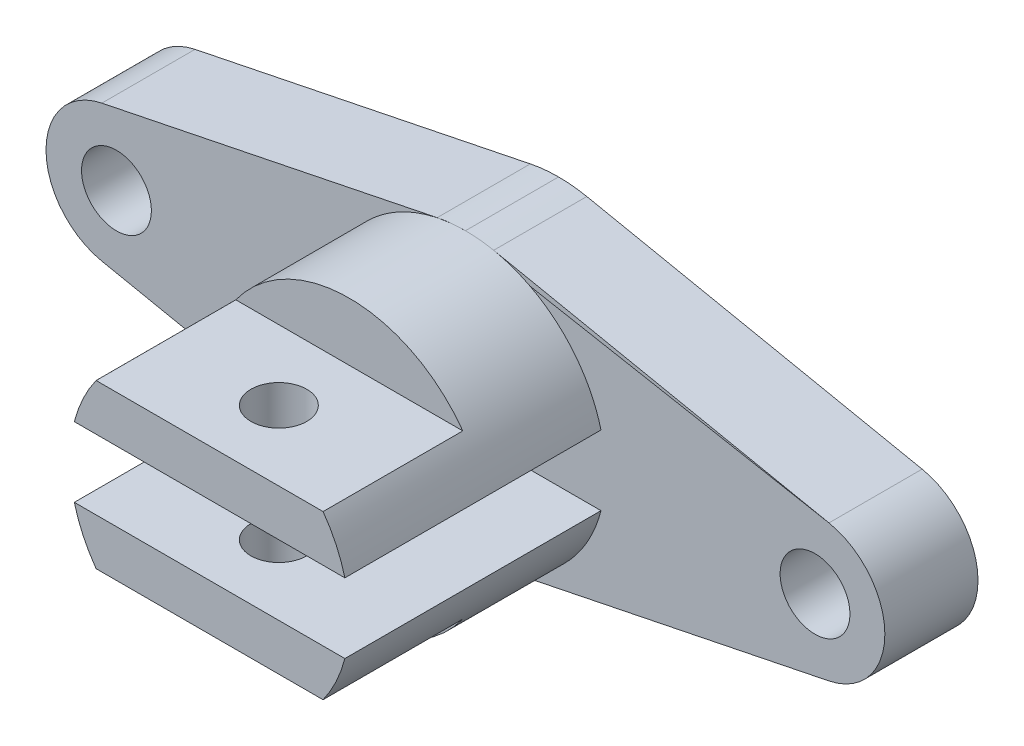
SolidWorks part; units mm, degrees
ref_plane "Alzado" through (0, 0, 0) normal (0, 0, 1) x (1, 0, 0)
ref_plane "Planta" through (0, 0, 0) normal (0, 1, 0) x (1, 0, 0)
ref_plane "Vista lateral" through (0, 0, 0) normal (1, 0, 0) x (0, 0, -1)
sketch "Croquis1" plane through (0, 0, 0) normal (0, 0, 1) x (1, 0, 0)
  line L0 (153, 14.6969) -> (81, 29.3939)
  line L1 (153, -14.6969) -> (81, -29.3939)
  line L4 (81, 29.3939) -> (81, -29.3939) construction
  line L5 (153, 14.6969) -> (153, -14.6969) construction
  line L10 (68.8736, 29.3678) -> (68.8736, -29.3678) construction
  line L11 (74.9354, 29.9999) -> (74.9354, -29.9999) construction
  line L12 (68.8709, 29.3939) -> (68.8709, -29.3939) construction
  line L13 (-3.1291, 14.6969) -> (68.8709, 29.3939)
  line L14 (-3.1291, 14.6969) -> (-3.1291, -14.6969) construction
  line L15 (-3.1291, -14.6969) -> (68.8709, -29.3939)
  circle A2 centre (150, 0) radius 7.5
  arc A7 (153, -14.6969) -> (153, 14.6969) centre (150, 0) ccw
  arc A8 (74.9354, -29.9999) -> (81, -29.3939) centre (75, 0) ccw
  arc A9 (81, 29.3939) -> (74.9354, 29.9999) centre (75, 0) ccw
  circle A10 centre (-0.1291, 0) radius 7.5
  arc A11 (-3.1291, -14.6969) -> (-3.1291, 14.6969) centre (-0.1291, 0) cw
  arc A12 (74.9354, -29.9999) -> (68.8709, -29.3939) centre (74.8709, 0) cw
  arc A13 (68.8709, 29.3939) -> (74.9354, 29.9999) centre (74.8709, 0) cw
  point P8 (-0.1291, 0)
  dimension "D2" = 15
  dimension "D6" = 60
  dimension "D5" = 30
  dimension "D7" = 75
extrude "Saliente-Extruir1" add sketch "Croquis1" along normal blind 20 contours L13 A13 A9 L0 A7 L1 A8 A12 L15 A11
sketch "Croquis3" plane through (0, 0, 20) normal (0, 0, 1) x (1, 0, 0)
  line L1 (45.9527, 7.5) -> (104.0473, 7.5)
  line L3 (45.9527, -7.5) -> (104.0473, -7.5)
  arc A0 (45.9527, -7.5) -> (104.0473, -7.5) centre (75, 0) ccw
  arc A1 (104.0473, 7.5) -> (45.9527, 7.5) centre (75, 0) ccw
  arc A2 (153, -14.6969) -> (153, 14.6969) centre (150, 0) ccw construction
  dimension "D1" = 75
  dimension "D2" = 15
  dimension "D3" = 75
  dimension "D4" = 30
extrude "Saliente-Extruir3" add sketch "Croquis3" along normal blind 55
sketch "Croquis9" plane through (0, 0, 75) normal (0, 0, 1) x (1, 0, 0)
  line L1 (74.9666, -0.0068) -> (75.0027, -0.0005) construction
  line L2 (50.6312, 17.4932) -> (99.3742, 17.4932)
  line L8 (75, -0.0068) -> (75.0027, -0.0005) construction
  line L9 (50.6402, -17.5068) -> (99.3652, -17.5068)
  line L11 (50.6312, 17.4932) -> (50.6312, 40.3381)
  line L12 (50.6312, 40.3381) -> (99.3742, 40.3381)
  line L13 (74.9666, -0.0068) -> (75, -0.0068) construction
  line L14 (99.3742, 40.3381) -> (99.3742, 17.4932)
  arc A5 (50.6402, -17.5068) -> (99.3652, -17.5068) centre (75.0027, -0.0005) ccw
  dimension "D2" = 17.5
  dimension "D1" = 60
  dimension "D3" = 75
  dimension "D4" = 17.5
  dimension "D6" = 30
extrude "Cortar-Extruir5" cut sketch "Croquis9" against normal blind 30
sketch "Croquis11" plane through (0, 0, 75) normal (0, 0, 1) x (1, 0, 0)
  line L0 (75.0011, -17.5068) -> (46.4166, -17.5068)
  line L1 (99.362, -17.5068) -> (50.6402, -17.5068) construction
  line L2 (46.4166, -17.5068) -> (46.4166, -38.5349)
  line L3 (46.4166, -38.5349) -> (75.0011, -38.5349)
  line L4 (75.0011, -38.5349) -> (75.0011, -17.5068)
extrude "Cortar-Extruir6" cut sketch "Croquis11" against normal blind 30
sketch "Croquis12" plane through (0, 17.4932, 0) normal (0, 1, 0) x (1, 0, 0)
  line L0 (-15.1291, 0) -> (-15.1291, -20) construction
  circle A0 centre (74.8709, -60) radius 6
  dimension "D1" = 12
  dimension "D2" = 90
  dimension "D3" = 60
extrude "Cortar-Extruir7" cut sketch "Croquis12" against normal blind 56
sketch "Croquis13" plane through (0, 0, 20) normal (0, 0, 1) x (1, 0, 0)
  line L0 (75.0026, 29.9999) -> (75, -29.9999) construction
  circle A0 centre (0, 0) radius 7.5
  arc A1 (99.3718, 17.4932) -> (50.6312, 17.4973) centre (75, 0) ccw construction
  arc A2 (50.638, -17.5068) -> (99.362, -17.5068) centre (75, 0) ccw construction
  circle A3 centre (150.0026, -0.0064) radius 7.5
  dimension "D1" = 15
extrude "Cortar-Extruir8" cut sketch "Croquis13" against normal blind 56 contours A0 | A3
